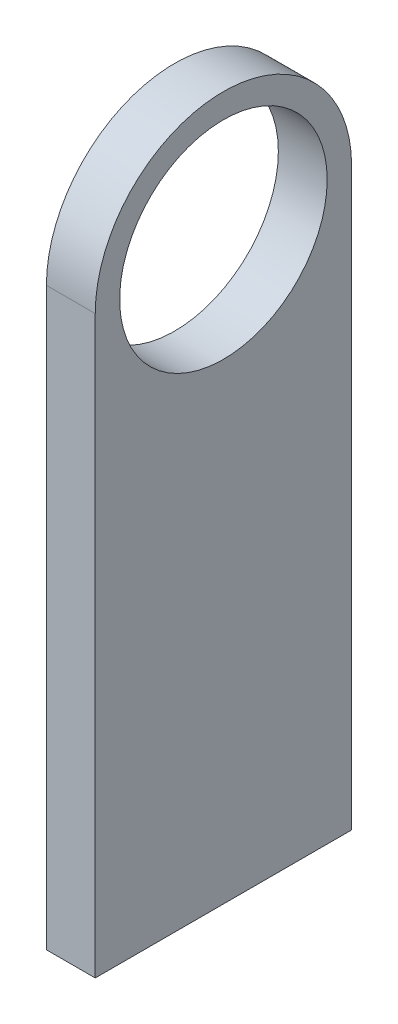
SolidWorks part; units mm, degrees
ref_plane "Front" through (0, 0, 0) normal (0, 0, 1) x (1, 0, 0)
ref_plane "Top" through (0, 0, 0) normal (0, 1, 0) x (1, 0, 0)
ref_plane "Right" through (0, 0, 0) normal (1, 0, 0) x (0, 0, -1)
sketch "Sketch1" plane through (0, 0, 0) normal (1, 0, 0) x (0, 0, -1)
  line L0 (0, 0) -> (0, -47.1379) construction
  line L1 (10.5, 0) -> (10.5, -47.1379)
  line L2 (-10.5, 0) -> (-10.5, -47.1379)
  line L3 (-10.5, -47.1379) -> (10.5, -47.1379)
  circle A0 centre (0, 0) radius 8.5
  arc A1 (10.5, 0) -> (-10.5, 0) centre (0, 0) ccw
  arc A2 (-4.903, -6.9434) -> (4.903, 6.9434) centre (0, 0) ccw construction
  dimension "D2" = 2
extrude "Boss-Extrude1" add sketch "Sketch1" along normal blind 4
